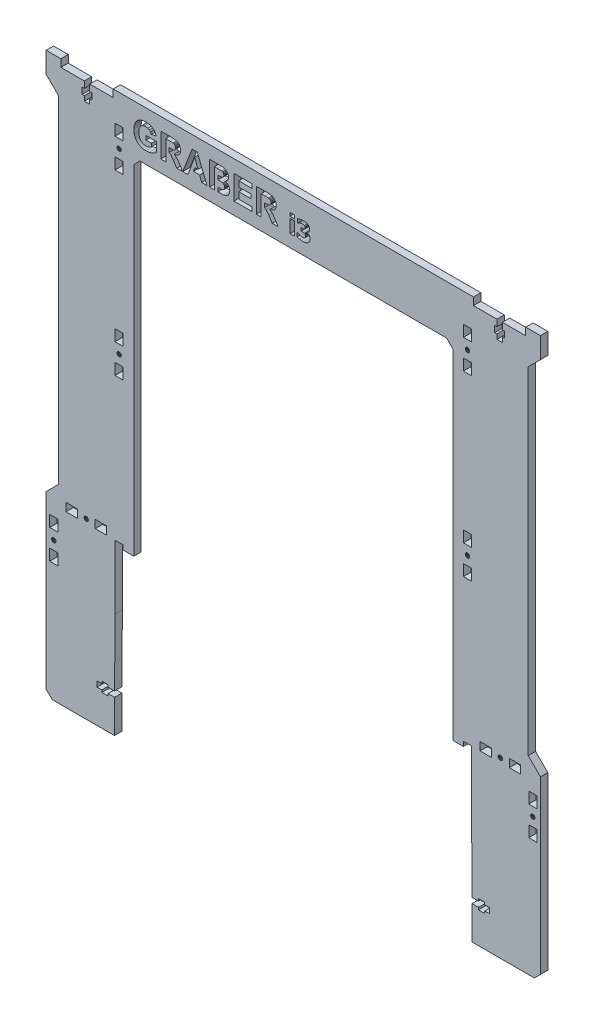
SolidWorks part; units mm, degrees
material "Maple"
ref_plane "Front Plane" through (0, 0, 0) normal (0, 0, 1) x (1, 0, 0)
ref_plane "Top Plane" through (0, 0, 0) normal (0, 1, 0) x (1, 0, 0)
ref_plane "Right Plane" through (0, 0, 0) normal (1, 0, 0) x (0, 0, -1)
sketch "Sketch1" plane through (0, 0, 0) normal (0, 0, 1) x (1, 0, 0)
  line L3495 (502.4777, 83.0503) -> (493.8277, 83.0503)
  line L3496 (509.2276, 34.5503) -> (509.5016, -19.959)
  line L3497 (218.4777, 34.5503) -> (218.4777, 86.741)
  line L3498 (218.4777, 86.741) -> (225.1777, 86.741)
  line L3499 (167.3778, -51.459) -> (162.3778, -46.6507)
  line L3500 (565.3276, -46.459) -> (560.3276, -51.459)
  line L3501 (233.8277, 359.5409) -> (238.8277, 364.5409)
  line L3502 (238.8277, 364.5409) -> (488.8277, 364.5409)
  line L3503 (488.8277, 364.5409) -> (493.8277, 359.5409)
  line L3504 (493.8277, 359.5409) -> (493.8277, 83.0503)
  line L3505 (534.2276, 398.4409) -> (553.3276, 398.4409)
  line L3506 (553.3276, 398.4409) -> (553.3276, 404.5409)
  line L3507 (191.6777, 393.1409) -> (191.6777, 388.0409)
  line L3508 (197.8777, 398.4409) -> (216.9777, 398.4409)
  line L3509 (529.8276, 393.1409) -> (528.0276, 393.1409)
  line L3510 (536.0276, 393.1409) -> (534.2276, 393.1409)
  line L3511 (553.3276, 404.5409) -> (565.3276, 404.5409)
  line L3512 (216.9777, 398.4409) -> (216.9777, 404.5409)
  line L3513 (529.8276, 388.0409) -> (529.8276, 384.0909)
  line L3514 (534.2276, 384.0909) -> (534.2276, 388.0409)
  line L3515 (528.0276, 393.1409) -> (528.0276, 388.0409)
  line L3516 (510.7276, 404.5409) -> (510.7276, 398.4409)
  line L3517 (510.7276, 398.4409) -> (529.8276, 398.4409)
  line L3518 (528.0276, 388.0409) -> (529.8276, 388.0409)
  line L3519 (529.8276, 384.0909) -> (534.2276, 384.0909)
  line L3520 (534.2276, 388.0409) -> (536.0276, 388.0409)
  line L3521 (529.8276, 398.4409) -> (529.8276, 393.1409)
  line L3522 (534.2276, 393.1409) -> (534.2276, 398.4409)
  line L3523 (536.0276, 388.0409) -> (536.0276, 393.1409)
  line L3524 (565.3276, 404.5409) -> (565.3276, 387.5409)
  line L3525 (560.3276, -51.459) -> (509.6276, -51.459)
  line L3526 (199.6777, 393.1409) -> (197.8777, 393.1409)
  line L3527 (193.4777, 398.4409) -> (193.4777, 393.1409)
  line L3528 (197.8777, 388.0409) -> (199.6777, 388.0409)
  line L3529 (197.8777, 393.1409) -> (197.8777, 398.4409)
  line L3530 (193.4777, 384.0909) -> (197.8777, 384.0909)
  line L3531 (199.6777, 388.0409) -> (199.6777, 393.1409)
  line L3532 (193.4777, 388.0409) -> (193.4777, 384.0909)
  line L3533 (197.8777, 384.0909) -> (197.8777, 388.0409)
  line L3534 (193.4777, 393.1409) -> (191.6777, 393.1409)
  line L3535 (191.6777, 388.0409) -> (193.4777, 388.0409)
  line L3536 (162.3778, -46.6507) -> (162.3778, 93.041)
  line L3537 (162.3778, 404.5409) -> (174.3778, 404.5409)
  line L3538 (174.3778, 398.4409) -> (193.4777, 398.4409)
  line L3539 (174.3778, 404.5409) -> (174.3778, 398.4409)
  line L3540 (216.9777, 404.5409) -> (510.7276, 404.5409)
  line L3541 (225.1777, 86.741) -> (225.1777, 83.0503)
  line L3542 (233.8277, 83.0503) -> (233.8277, 359.5409)
  line L3543 (225.1777, 83.0503) -> (233.8277, 83.0503)
  line L3544 (509.2276, 34.5503) -> (509.2276, 86.741)
  line L3545 (509.2276, 86.741) -> (502.4777, 86.741)
  line L3546 (502.4777, 86.741) -> (502.4777, 83.0503)
  line L3547 (218.0277, -51.459) -> (167.3778, -51.459)
  line L3548 (218.4777, 34.5503) -> (218.1695, -19.959)
  line L3549 (162.3778, 93.041) -> (172.3778, 103.041)
  line L3550 (162.3778, 387.5409) -> (162.3778, 404.5409)
  line L3551 (162.3778, 387.5409) -> (172.3778, 377.5409)
  line L3552 (172.3778, 377.5409) -> (172.3778, 103.041)
  line L3553 (565.3276, 93.041) -> (565.3276, -46.459)
  line L3554 (565.3276, 93.041) -> (555.3276, 103.041)
  line L3555 (555.3276, 103.041) -> (555.3276, 377.5409)
  line L3556 (555.3276, 377.5409) -> (565.3276, 387.5409)
  line L3557 (223.1018, 365.9091) -> (222.7286, 366.1955)
  line L3558 (223.3881, 365.536) -> (223.1018, 365.9091)
  line L3559 (223.5681, 365.1015) -> (223.3881, 365.536)
  line L3560 (223.5681, 364.1688) -> (223.6295, 364.6351)
  line L3561 (223.3881, 363.7343) -> (223.5681, 364.1688)
  line L3562 (223.1018, 363.3611) -> (223.3881, 363.7343)
  line L3563 (222.7286, 363.0748) -> (223.1018, 363.3611)
  line L3564 (222.2941, 362.8948) -> (222.7286, 363.0748)
  line L3565 (221.8277, 362.8334) -> (222.2941, 362.8948)
  line L3566 (220.026, 219.5502) -> (220.0874, 219.0839)
  line L3567 (221.3614, 217.8099) -> (221.8277, 217.7485)
  line L3568 (220.9269, 217.9899) -> (221.3614, 217.8099)
  line L3569 (507.568, 364.1688) -> (507.6294, 364.6351)
  line L3570 (507.388, 363.7343) -> (507.568, 364.1688)
  line L3571 (507.1017, 363.3611) -> (507.388, 363.7343)
  line L3572 (506.7285, 363.0748) -> (507.1017, 363.3611)
  line L3573 (506.294, 362.8948) -> (506.7285, 363.0748)
  line L3574 (505.8277, 362.8334) -> (506.294, 362.8948)
  line L3575 (220.0874, 365.1015) -> (220.026, 364.6351)
  line L3576 (220.2674, 365.536) -> (220.0874, 365.1015)
  line L3577 (187.7778, 86.791) -> (187.7778, 93.3909)
  line L3578 (202.3777, 93.3909) -> (202.3777, 86.791)
  line L3579 (202.3777, 86.791) -> (211.5777, 86.791)
  line L3580 (562.3776, 45.291) -> (562.3776, 54.491)
  line L3581 (218.5277, 357.3351) -> (218.5277, 348.1351)
  line L3582 (225.1277, 371.9351) -> (225.1277, 381.1351)
  line L3583 (559.544, 63.5313) -> (559.0776, 63.5927)
  line L3584 (558.1768, 60.2306) -> (558.6113, 60.0506)
  line L3585 (170.3181, 61.3246) -> (170.3795, 61.791)
  line L3586 (167.0174, 62.6918) -> (166.8374, 62.2573)
  line L3587 (168.5778, 63.5927) -> (168.1114, 63.5313)
  line L3588 (169.8518, 63.065) -> (169.4786, 63.3513)
  line L3589 (193.3374, 89.6246) -> (193.5174, 89.1901)
  line L3590 (195.9786, 91.6513) -> (195.5441, 91.8313)
  line L3591 (560.8794, 61.791) -> (560.818, 62.2573)
  line L3592 (170.3795, 61.791) -> (170.3181, 62.2573)
  line L3593 (166.8374, 62.2573) -> (166.776, 61.791)
  line L3594 (559.0776, 63.5927) -> (558.6113, 63.5313)
  line L3595 (169.4786, 63.3513) -> (169.0441, 63.5313)
  line L3596 (167.3037, 60.5169) -> (167.6769, 60.2306)
  line L3597 (559.0776, 59.9892) -> (559.544, 60.0506)
  line L3598 (168.1114, 60.0506) -> (168.5778, 59.9892)
  line L3599 (558.6113, 63.5313) -> (558.1768, 63.3513)
  line L3600 (559.9785, 63.3513) -> (559.544, 63.5313)
  line L3601 (170.1381, 62.6918) -> (169.8518, 63.065)
  line L3602 (560.818, 61.3246) -> (560.8794, 61.791)
  line L3603 (271.9766, 388.6925) -> (271.8953, 387.6341)
  line L3604 (271.8953, 387.6341) -> (271.6513, 386.672)
  line L3605 (271.6513, 386.672) -> (271.2447, 385.8064)
  line L3606 (271.2447, 385.8064) -> (270.6755, 385.0372)
  line L3607 (225.1277, 381.1351) -> (218.5277, 381.1351)
  line L3608 (218.5277, 381.1351) -> (218.5277, 371.9351)
  line L3609 (218.5277, 371.9351) -> (225.1277, 371.9351)
  line L3610 (218.5277, 348.1351) -> (225.1277, 348.1351)
  line L3611 (225.1277, 348.1351) -> (225.1277, 357.3351)
  line L3612 (225.1277, 357.3351) -> (218.5277, 357.3351)
  line L3613 (225.1277, 236.0502) -> (218.5277, 236.0502)
  line L3614 (218.5277, 236.0502) -> (218.5277, 226.8502)
  line L3615 (218.5277, 226.8502) -> (225.1277, 226.8502)
  line L3616 (218.5277, 203.0502) -> (225.1277, 203.0502)
  line L3617 (225.1277, 203.0502) -> (225.1277, 212.2502)
  line L3618 (225.1277, 212.2502) -> (218.5277, 212.2502)
  line L3619 (218.5277, 212.2502) -> (218.5277, 203.0502)
  line L3620 (533.9016, 91.365) -> (533.5285, 91.6513)
  line L3621 (557.8036, 63.065) -> (557.5173, 62.6918)
  line L3622 (196.8181, 90.5573) -> (196.6381, 90.9918)
  line L3623 (195.0777, 88.2892) -> (195.5441, 88.3506)
  line L3624 (193.8037, 88.8169) -> (194.1769, 88.5306)
  line L3625 (532.6276, 91.8927) -> (532.1613, 91.8313)
  line L3626 (531.3536, 91.365) -> (531.0673, 90.9918)
  line L3627 (532.1613, 91.8313) -> (531.7268, 91.6513)
  line L3628 (557.8036, 60.5169) -> (558.1768, 60.2306)
  line L3629 (559.9785, 60.2306) -> (560.3516, 60.5169)
  line L3630 (560.818, 62.2573) -> (560.638, 62.6918)
  line L3631 (165.2778, 45.291) -> (171.8778, 45.291)
  line L3632 (171.8778, 69.091) -> (171.8778, 78.291)
  line L3633 (171.8778, 78.291) -> (165.2778, 78.291)
  line L3634 (165.2778, 78.291) -> (165.2778, 69.091)
  line L3635 (165.2778, 69.091) -> (171.8778, 69.091)
  line L3636 (187.7778, 93.3909) -> (178.5778, 93.3909)
  line L3637 (178.5778, 93.3909) -> (178.5778, 86.791)
  line L3638 (178.5778, 86.791) -> (187.7778, 86.791)
  line L3639 (220.9269, 366.1955) -> (220.5537, 365.9091)
  line L3640 (221.3614, 366.3755) -> (220.9269, 366.1955)
  line L3641 (221.8277, 366.4369) -> (221.3614, 366.3755)
  line L3642 (220.026, 364.6351) -> (220.0874, 364.1688)
  line L3643 (221.3614, 362.8948) -> (221.8277, 362.8334)
  line L3644 (220.9269, 363.0748) -> (221.3614, 362.8948)
  line L3645 (220.5537, 363.3611) -> (220.9269, 363.0748)
  line L3646 (220.2674, 363.7343) -> (220.5537, 363.3611)
  line L3647 (220.0874, 364.1688) -> (220.2674, 363.7343)
  line L3648 (223.6295, 364.6351) -> (223.5681, 365.1015)
  line L3649 (222.2941, 366.3755) -> (221.8277, 366.4369)
  line L3650 (222.7286, 366.1955) -> (222.2941, 366.3755)
  line L3651 (220.5537, 218.2762) -> (220.9269, 217.9899)
  line L3652 (220.2674, 218.6493) -> (220.5537, 218.2762)
  line L3653 (220.0874, 219.0839) -> (220.2674, 218.6493)
  line L3654 (223.6295, 219.5502) -> (223.5681, 220.0165)
  line L3655 (222.2941, 221.2905) -> (221.8277, 221.3519)
  line L3656 (222.7286, 221.1106) -> (222.2941, 221.2905)
  line L3657 (223.1018, 220.8242) -> (222.7286, 221.1106)
  line L3658 (223.3881, 220.4511) -> (223.1018, 220.8242)
  line L3659 (223.5681, 220.0165) -> (223.3881, 220.4511)
  line L3660 (220.0874, 220.0165) -> (220.026, 219.5502)
  line L3661 (220.2674, 220.4511) -> (220.0874, 220.0165)
  line L3662 (220.5537, 220.8242) -> (220.2674, 220.4511)
  line L3663 (220.9269, 221.1106) -> (220.5537, 220.8242)
  line L3664 (221.3614, 221.2905) -> (220.9269, 221.1106)
  line L3665 (221.8277, 221.3519) -> (221.3614, 221.2905)
  line L3666 (223.5681, 219.0839) -> (223.6295, 219.5502)
  line L3667 (223.3881, 218.6493) -> (223.5681, 219.0839)
  line L3668 (516.1276, 93.3909) -> (516.1276, 86.791)
  line L3669 (516.1276, 86.791) -> (525.3276, 86.791)
  line L3670 (525.3276, 86.791) -> (525.3276, 93.3909)
  line L3671 (525.3276, 93.3909) -> (516.1276, 93.3909)
  line L3672 (539.9276, 86.791) -> (549.1276, 86.791)
  line L3673 (167.3037, 63.065) -> (167.0174, 62.6918)
  line L3674 (166.776, 61.791) -> (166.8374, 61.3246)
  line L3675 (168.5778, 59.9892) -> (169.0441, 60.0506)
  line L3676 (169.0441, 63.5313) -> (168.5778, 63.5927)
  line L3677 (168.1114, 63.5313) -> (167.6769, 63.3513)
  line L3678 (196.3518, 88.8169) -> (196.6381, 89.1901)
  line L3679 (194.1769, 91.6513) -> (193.8037, 91.365)
  line L3680 (211.5777, 86.791) -> (211.5777, 93.3909)
  line L3681 (549.1276, 86.791) -> (549.1276, 93.3909)
  line L3682 (549.1276, 93.3909) -> (539.9276, 93.3909)
  line L3683 (539.9276, 93.3909) -> (539.9276, 86.791)
  line L3684 (562.3776, 78.291) -> (555.7776, 78.291)
  line L3685 (171.8778, 54.491) -> (165.2778, 54.491)
  line L3686 (165.2778, 54.491) -> (165.2778, 45.291)
  line L3687 (558.1768, 63.3513) -> (557.8036, 63.065)
  line L3688 (169.4786, 60.2306) -> (169.8518, 60.5169)
  line L3689 (557.2759, 61.791) -> (557.3373, 61.3246)
  line L3690 (560.3516, 60.5169) -> (560.638, 60.8901)
  line L3691 (557.5173, 62.6918) -> (557.3373, 62.2573)
  line L3692 (560.3516, 63.065) -> (559.9785, 63.3513)
  line L3693 (558.6113, 60.0506) -> (559.0776, 59.9892)
  line L3694 (507.568, 220.0165) -> (507.388, 220.4511)
  line L3695 (504.0873, 220.0165) -> (504.0259, 219.5502)
  line L3696 (505.8277, 221.3519) -> (505.3613, 221.2905)
  line L3697 (507.568, 365.1015) -> (507.388, 365.536)
  line L3698 (507.6294, 364.6351) -> (507.568, 365.1015)
  line L3699 (506.294, 366.3755) -> (505.8277, 366.4369)
  line L3700 (506.7285, 366.1955) -> (506.294, 366.3755)
  line L3701 (507.1017, 365.9091) -> (506.7285, 366.1955)
  line L3702 (507.388, 365.536) -> (507.1017, 365.9091)
  line L3703 (504.2673, 363.7343) -> (504.5536, 363.3611)
  line L3704 (504.0259, 364.6351) -> (504.0873, 364.1688)
  line L3705 (505.8277, 366.4369) -> (505.3613, 366.3755)
  line L3706 (504.2673, 365.536) -> (504.0873, 365.1015)
  line L3707 (504.0873, 365.1015) -> (504.0259, 364.6351)
  line L3708 (505.3613, 366.3755) -> (504.9268, 366.1955)
  line L3709 (504.5536, 365.9091) -> (504.2673, 365.536)
  line L3710 (504.9268, 366.1955) -> (504.5536, 365.9091)
  line L3711 (505.3613, 362.8948) -> (505.8277, 362.8334)
  line L3712 (504.5536, 363.3611) -> (504.9268, 363.0748)
  line L3713 (504.0873, 364.1688) -> (504.2673, 363.7343)
  line L3714 (504.9268, 363.0748) -> (505.3613, 362.8948)
  line L3715 (225.1277, 226.8502) -> (225.1277, 236.0502)
  line L3716 (502.5276, 212.2502) -> (502.5276, 203.0502)
  line L3717 (509.1277, 236.0502) -> (502.5276, 236.0502)
  line L3718 (502.5276, 381.1351) -> (502.5276, 371.9351)
  line L3719 (502.5276, 371.9351) -> (509.1277, 371.9351)
  line L3720 (509.1277, 381.1351) -> (502.5276, 381.1351)
  line L3721 (509.1277, 226.8502) -> (509.1277, 236.0502)
  line L3722 (509.1277, 212.2502) -> (502.5276, 212.2502)
  line L3723 (502.5276, 226.8502) -> (509.1277, 226.8502)
  line L3724 (502.5276, 203.0502) -> (509.1277, 203.0502)
  line L3725 (502.5276, 236.0502) -> (502.5276, 226.8502)
  line L3726 (509.1277, 203.0502) -> (509.1277, 212.2502)
  line L3727 (195.5441, 88.3506) -> (195.9786, 88.5306)
  line L3728 (195.9786, 88.5306) -> (196.3518, 88.8169)
  line L3729 (531.0673, 90.9918) -> (530.8873, 90.5573)
  line L3730 (557.3373, 62.2573) -> (557.2759, 61.791)
  line L3731 (171.8778, 45.291) -> (171.8778, 54.491)
  line L3732 (211.5777, 93.3909) -> (202.3777, 93.3909)
  line L3733 (236.7016, 392.0091) -> (237.7186, 392.855)
  line L3734 (237.7186, 392.855) -> (238.8847, 393.5617)
  line L3735 (238.8847, 393.5617) -> (239.8883, 393.9901)
  line L3736 (239.8883, 393.9901) -> (241.0075, 394.2961)
  line L3737 (241.0075, 394.2961) -> (243.593, 394.5409)
  line L3738 (243.593, 394.5409) -> (245.3238, 394.4449)
  line L3739 (245.3238, 394.4449) -> (246.8542, 394.1569)
  line L3740 (246.8542, 394.1569) -> (248.1843, 393.677)
  line L3741 (248.1843, 393.677) -> (249.314, 393.005)
  line L3742 (249.314, 393.005) -> (250.2517, 392.1637)
  line L3743 (250.2517, 392.1637) -> (251.0058, 391.1757)
  line L3744 (251.0058, 391.1757) -> (251.5763, 390.041)
  line L3745 (251.5763, 390.041) -> (251.9632, 388.7596)
  line L3746 (251.9632, 388.7596) -> (248.0196, 388.0218)
  line L3747 (248.0196, 388.0218) -> (247.421, 389.3179)
  line L3748 (247.421, 389.3179) -> (246.4568, 390.3089)
  line L3749 (246.4568, 390.3089) -> (245.1674, 390.9376)
  line L3750 (245.1674, 390.9376) -> (243.593, 391.1472)
  line L3751 (243.593, 391.1472) -> (242.3585, 391.0441)
  line L3752 (242.3585, 391.0441) -> (241.2573, 390.7347)
  line L3753 (241.2573, 390.7347) -> (240.2894, 390.2192)
  line L3754 (240.2894, 390.2192) -> (239.4548, 389.4973)
  line L3755 (239.4548, 389.4973) -> (238.7829, 388.5726)
  line L3756 (238.7829, 388.5726) -> (238.3029, 387.4484)
  line L3757 (238.3029, 387.4484) -> (238.0149, 386.1246)
  line L3758 (238.0149, 386.1246) -> (237.919, 384.6013)
  line L3759 (237.919, 384.6013) -> (238.0162, 382.9602)
  line L3760 (238.0162, 382.9602) -> (238.308, 381.5379)
  line L3761 (238.308, 381.5379) -> (238.7942, 380.3344)
  line L3762 (238.7942, 380.3344) -> (239.475, 379.3498)
  line L3763 (239.475, 379.3498) -> (240.3133, 378.5839)
  line L3764 (240.3133, 378.5839) -> (241.2724, 378.0369)
  line L3765 (241.2724, 378.0369) -> (242.3522, 377.7087)
  line L3766 (242.3522, 377.7087) -> (243.5528, 377.5993)
  line L3767 (243.5528, 377.5993) -> (244.8019, 377.7217)
  line L3768 (244.8019, 377.7217) -> (246.0544, 378.0889)
  line L3769 (246.0544, 378.0889) -> (247.2198, 378.6305)
  line L3770 (247.2198, 378.6305) -> (248.2073, 379.276)
  line L3771 (248.2073, 379.276) -> (248.2073, 381.771)
  line L3772 (248.2073, 381.771) -> (243.6601, 381.771)
  line L3773 (243.6601, 381.771) -> (243.6601, 385.0842)
  line L3774 (243.6601, 385.0842) -> (252.2181, 385.0842)
  line L3775 (252.2181, 385.0842) -> (252.2181, 377.2505)
  line L3776 (252.2181, 377.2505) -> (250.6906, 376.1154)
  line L3777 (250.6906, 376.1154) -> (248.6031, 375.1244)
  line L3778 (248.6031, 375.1244) -> (246.2204, 374.4353)
  line L3779 (246.2204, 374.4353) -> (243.8076, 374.2056)
  line L3780 (243.8076, 374.2056) -> (242.3145, 374.2865)
  line L3781 (242.3145, 374.2865) -> (240.9203, 374.5292)
  line L3782 (240.9203, 374.5292) -> (239.625, 374.9337)
  line L3783 (239.625, 374.9337) -> (238.4287, 375.5)
  line L3784 (238.4287, 375.5) -> (237.3531, 376.2168)
  line L3785 (237.3531, 376.2168) -> (236.42, 377.0728)
  line L3786 (236.42, 377.0728) -> (235.6294, 378.0679)
  line L3787 (235.6294, 378.0679) -> (234.9813, 379.2022)
  line L3788 (234.9813, 379.2022) -> (234.4766, 380.4325)
  line L3789 (234.4766, 380.4325) -> (234.1161, 381.7156)
  line L3790 (234.1161, 381.7156) -> (233.8277, 384.4403)
  line L3791 (233.8277, 384.4403) -> (233.9082, 385.9334)
  line L3792 (233.9082, 385.9334) -> (234.1497, 387.3411)
  line L3793 (234.1497, 387.3411) -> (234.5521, 388.6632)
  line L3794 (234.5521, 388.6632) -> (235.1155, 389.8997)
  line L3795 (235.1155, 389.8997) -> (235.8339, 391.024)
  line L3796 (235.8339, 391.024) -> (236.7016, 392.0091)
  line L3797 (220.5537, 365.9091) -> (220.2674, 365.536)
  line L3798 (223.1018, 218.2762) -> (223.3881, 218.6493)
  line L3799 (222.7286, 217.9899) -> (223.1018, 218.2762)
  line L3800 (222.2941, 217.8099) -> (222.7286, 217.9899)
  line L3801 (221.8277, 217.7485) -> (222.2941, 217.8099)
  line L3802 (307.0538, 374.6751) -> (302.342, 374.5431)
  line L3803 (302.342, 377.8541) -> (302.342, 374.5431)
  line L3804 (302.342, 377.8541) -> (303.2174, 377.8541)
  line L3805 (303.2174, 377.8541) -> (305.9404, 377.9749)
  line L3806 (305.9404, 377.9749) -> (306.7436, 378.2515)
  line L3807 (306.7436, 378.2515) -> (307.3824, 378.7596)
  line L3808 (307.3824, 378.7596) -> (307.7999, 379.4889)
  line L3809 (307.7999, 379.4889) -> (307.9391, 380.4296)
  line L3810 (307.9391, 380.4296) -> (307.8318, 381.2478)
  line L3811 (307.8318, 381.2478) -> (307.5098, 381.9319)
  line L3812 (307.5098, 381.9319) -> (306.985, 382.4651)
  line L3813 (306.985, 382.4651) -> (306.2691, 382.8307)
  line L3814 (306.2691, 382.8307) -> (304.983, 383.0419)
  line L3815 (304.983, 383.0419) -> (302.7479, 383.1123)
  line L3816 (302.7479, 383.1123) -> (302.342, 383.1123)
  line L3817 (302.342, 383.1123) -> (302.342, 386.3899)
  line L3818 (302.342, 386.3899) -> (305.0283, 386.4524)
  line L3819 (305.0283, 386.4524) -> (305.9387, 386.6888)
  line L3820 (305.9387, 386.6888) -> (306.6312, 387.1566)
  line L3821 (306.6312, 387.1566) -> (307.0689, 387.8323)
  line L3822 (307.0689, 387.8323) -> (307.2147, 388.6925)
  line L3823 (307.2147, 388.6925) -> (307.089, 389.5191)
  line L3824 (307.089, 389.5191) -> (306.7117, 390.1747)
  line L3825 (306.7117, 390.1747) -> (306.0863, 390.6325)
  line L3826 (306.0863, 390.6325) -> (305.2161, 390.8655)
  line L3827 (305.2161, 390.8655) -> (301.8224, 390.9326)
  line L3828 (301.8224, 390.9326) -> (299.542, 390.9326)
  line L3829 (299.542, 390.9326) -> (299.542, 374.5409)
  line L3830 (299.542, 374.5409) -> (295.5715, 374.5409)
  line L3831 (295.5715, 374.5409) -> (295.5715, 394.2056)
  line L3832 (295.5715, 394.2056) -> (303.432, 394.2056)
  line L3833 (303.432, 394.2056) -> (306.9129, 394.0111)
  line L3834 (306.9129, 394.0111) -> (307.9994, 393.7109)
  line L3835 (307.9994, 393.7109) -> (308.9652, 393.1995)
  line L3836 (308.9652, 393.1995) -> (309.7952, 392.4802)
  line L3837 (309.7952, 392.4802) -> (310.4743, 391.5563)
  line L3838 (310.4743, 391.5563) -> (310.927, 390.4681)
  line L3839 (310.927, 390.4681) -> (311.0779, 389.2559)
  line L3840 (311.0779, 389.2559) -> (310.8918, 387.9313)
  line L3841 (310.8918, 387.9313) -> (310.3334, 386.7207)
  line L3842 (310.3334, 386.7207) -> (309.4565, 385.7113)
  line L3843 (309.4565, 385.7113) -> (308.3147, 384.9903)
  line L3844 (308.3147, 384.9903) -> (309.9042, 384.2827)
  line L3845 (309.9042, 384.2827) -> (311.0779, 383.2062)
  line L3846 (311.0779, 383.2062) -> (311.8023, 381.8347)
  line L3847 (311.8023, 381.8347) -> (312.0437, 380.2418)
  line L3848 (312.0437, 380.2418) -> (311.8878, 378.9189)
  line L3849 (311.8878, 378.9189) -> (311.42, 377.6328)
  line L3850 (311.42, 377.6328) -> (310.6822, 376.4926)
  line L3851 (310.6822, 376.4926) -> (309.7164, 375.6073)
  line L3852 (309.7164, 375.6073) -> (308.5108, 374.9953)
  line L3853 (308.5108, 374.9953) -> (307.0538, 374.6751)
  line L3854 (341.1215, 382.2136) -> (340.5078, 382.5288)
  line L3855 (340.5043, 385.889) -> (340.5078, 382.5288)
  line L3856 (340.5043, 385.889) -> (340.642, 385.889)
  line L3857 (340.642, 385.889) -> (342.9625, 385.9494)
  line L3858 (342.9625, 385.9494) -> (344.21, 386.1305)
  line L3859 (344.21, 386.1305) -> (344.8438, 386.4591)
  line L3860 (344.8438, 386.4591) -> (345.3234, 386.9621)
  line L3861 (345.3234, 386.9621) -> (345.6252, 387.6261)
  line L3862 (345.6252, 387.6261) -> (345.7258, 388.4376)
  line L3863 (345.7258, 388.4376) -> (345.5933, 389.3347)
  line L3864 (345.5933, 389.3347) -> (345.1959, 390.0406)
  line L3865 (345.1959, 390.0406) -> (344.5571, 390.5386)
  line L3866 (344.5571, 390.5386) -> (343.7003, 390.8119)
  line L3867 (343.7003, 390.8119) -> (340.8029, 390.8789)
  line L3868 (340.8029, 390.8789) -> (337.7043, 390.8789)
  line L3869 (337.7043, 390.8789) -> (337.7043, 374.5409)
  line L3870 (337.7043, 374.5409) -> (333.7338, 374.5409)
  line L3871 (333.7338, 374.5409) -> (333.7338, 394.2056)
  line L3872 (333.7338, 394.2056) -> (342.0906, 394.2056)
  line L3873 (342.0906, 394.2056) -> (344.812, 394.0731)
  line L3874 (344.812, 394.0731) -> (346.6715, 393.6757)
  line L3875 (346.6715, 393.6757) -> (347.9575, 392.9396)
  line L3876 (347.9575, 392.9396) -> (348.9585, 391.7911)
  line L3877 (348.9585, 391.7911) -> (349.6024, 390.339)
  line L3878 (349.6024, 390.339) -> (349.817, 388.6925)
  line L3879 (349.817, 388.6925) -> (349.7357, 387.6341)
  line L3880 (349.7357, 387.6341) -> (349.4917, 386.672)
  line L3881 (349.4917, 386.672) -> (349.0851, 385.8064)
  line L3882 (349.0851, 385.8064) -> (348.5159, 385.0372)
  line L3883 (348.5159, 385.0372) -> (347.7848, 384.3829)
  line L3884 (347.7848, 384.3829) -> (346.8928, 383.8618)
  line L3885 (346.8928, 383.8618) -> (345.8398, 383.4741)
  line L3886 (345.8398, 383.4741) -> (344.6259, 383.2197)
  line L3887 (344.6259, 383.2197) -> (345.8012, 382.4316)
  line L3888 (345.8012, 382.4316) -> (346.7519, 381.5698)
  line L3889 (346.7519, 381.5698) -> (347.7362, 380.3223)
  line L3890 (347.7362, 380.3223) -> (349.0122, 378.3773)
  line L3891 (349.0122, 378.3773) -> (351.4133, 374.5409)
  line L3892 (351.4133, 374.5409) -> (346.6648, 374.5409)
  line L3893 (346.6648, 374.5409) -> (343.7942, 378.8199)
  line L3894 (343.7942, 378.8199) -> (341.7016, 381.7106)
  line L3895 (341.7016, 381.7106) -> (341.1215, 382.2136)
  line L3896 (282.354, 379.0077) -> (283.5747, 382.3209)
  line L3897 (283.5747, 382.3209) -> (286.1416, 382.3209)
  line L3898 (286.1416, 382.3209) -> (283.432, 389.618)
  line L3899 (283.432, 389.618) -> (277.9324, 374.5409)
  line L3900 (277.9324, 374.5409) -> (273.7204, 374.5409)
  line L3901 (273.7204, 374.5409) -> (281.3797, 394.2056)
  line L3902 (281.3797, 394.2056) -> (285.5782, 394.2056)
  line L3903 (285.5782, 394.2056) -> (293.4522, 374.5409)
  line L3904 (293.4522, 374.5409) -> (289.1329, 374.5409)
  line L3905 (289.1329, 374.5409) -> (287.4159, 379.0077)
  line L3906 (287.4159, 379.0077) -> (282.354, 379.0077)
  line L3907 (555.7776, 45.291) -> (562.3776, 45.291)
  line L3908 (555.7776, 54.491) -> (555.7776, 45.291)
  line L3909 (562.3776, 54.491) -> (555.7776, 54.491)
  line L3910 (560.638, 62.6918) -> (560.3516, 63.065)
  line L3911 (560.638, 60.8901) -> (560.818, 61.3246)
  line L3912 (559.544, 60.0506) -> (559.9785, 60.2306)
  line L3913 (557.5173, 60.8901) -> (557.8036, 60.5169)
  line L3914 (557.3373, 61.3246) -> (557.5173, 60.8901)
  line L3915 (170.1381, 60.8901) -> (170.3181, 61.3246)
  line L3916 (169.8518, 60.5169) -> (170.1381, 60.8901)
  line L3917 (169.0441, 60.0506) -> (169.4786, 60.2306)
  line L3918 (167.6769, 60.2306) -> (168.1114, 60.0506)
  line L3919 (167.0174, 60.8901) -> (167.3037, 60.5169)
  line L3920 (166.8374, 61.3246) -> (167.0174, 60.8901)
  line L3921 (167.6769, 63.3513) -> (167.3037, 63.065)
  line L3922 (170.3181, 62.2573) -> (170.1381, 62.6918)
  line L3923 (193.276, 90.0909) -> (193.3374, 89.6246)
  line L3924 (193.3374, 90.5573) -> (193.276, 90.0909)
  line L3925 (193.5174, 90.9918) -> (193.3374, 90.5573)
  line L3926 (193.8037, 91.365) -> (193.5174, 90.9918)
  line L3927 (194.6114, 91.8313) -> (194.1769, 91.6513)
  line L3928 (195.0777, 91.8927) -> (194.6114, 91.8313)
  line L3929 (195.5441, 91.8313) -> (195.0777, 91.8927)
  line L3930 (196.3518, 91.365) -> (195.9786, 91.6513)
  line L3931 (196.6381, 90.9918) -> (196.3518, 91.365)
  line L3932 (196.8795, 90.0909) -> (196.8181, 90.5573)
  line L3933 (196.8181, 89.6246) -> (196.8795, 90.0909)
  line L3934 (196.6381, 89.1901) -> (196.8181, 89.6246)
  line L3935 (194.6114, 88.3506) -> (195.0777, 88.2892)
  line L3936 (194.1769, 88.5306) -> (194.6114, 88.3506)
  line L3937 (193.5174, 89.1901) -> (193.8037, 88.8169)
  line L3938 (330.3536, 374.5409) -> (315.3972, 374.5409)
  line L3939 (315.3972, 374.5409) -> (315.3972, 394.2056)
  line L3940 (315.3972, 394.2056) -> (329.978, 394.2056)
  line L3941 (329.978, 394.2056) -> (329.978, 390.8789)
  line L3942 (329.978, 390.8789) -> (319.3676, 390.8789)
  line L3943 (319.3676, 390.8789) -> (319.3676, 386.5195)
  line L3944 (319.3676, 386.5195) -> (329.2402, 386.5195)
  line L3945 (329.2402, 386.5195) -> (329.2402, 383.2062)
  line L3946 (329.2402, 383.2062) -> (319.3676, 383.2062)
  line L3947 (319.3676, 383.2062) -> (319.3676, 377.8541)
  line L3948 (319.3676, 377.8541) -> (330.3536, 377.8541)
  line L3949 (330.3536, 377.8541) -> (330.3536, 374.5409)
  line L3950 (534.188, 90.9918) -> (533.9016, 91.365)
  line L3951 (534.368, 90.5573) -> (534.188, 90.9918)
  line L3952 (534.4294, 90.0909) -> (534.368, 90.5573)
  line L3953 (534.368, 89.6246) -> (534.4294, 90.0909)
  line L3954 (534.188, 89.1901) -> (534.368, 89.6246)
  line L3955 (533.9016, 88.8169) -> (534.188, 89.1901)
  line L3956 (533.5285, 88.5306) -> (533.9016, 88.8169)
  line L3957 (533.094, 88.3506) -> (533.5285, 88.5306)
  line L3958 (532.6276, 88.2892) -> (533.094, 88.3506)
  line L3959 (532.1613, 88.3506) -> (532.6276, 88.2892)
  line L3960 (531.7268, 88.5306) -> (532.1613, 88.3506)
  line L3961 (531.3536, 88.8169) -> (531.7268, 88.5306)
  line L3962 (531.0673, 89.1901) -> (531.3536, 88.8169)
  line L3963 (530.8873, 89.6246) -> (531.0673, 89.1901)
  line L3964 (530.8259, 90.0909) -> (530.8873, 89.6246)
  line L3965 (530.8873, 90.5573) -> (530.8259, 90.0909)
  line L3966 (531.7268, 91.6513) -> (531.3536, 91.365)
  line L3967 (533.094, 91.8313) -> (532.6276, 91.8927)
  line L3968 (533.5285, 91.6513) -> (533.094, 91.8313)
  line L3969 (562.3776, 69.091) -> (562.3776, 78.291)
  line L3970 (555.7776, 69.091) -> (562.3776, 69.091)
  line L3971 (555.7776, 78.291) -> (555.7776, 69.091)
  line L3972 (507.6294, 219.5502) -> (507.568, 220.0165)
  line L3973 (507.568, 219.0839) -> (507.6294, 219.5502)
  line L3974 (507.388, 218.6493) -> (507.568, 219.0839)
  line L3975 (507.1017, 218.2762) -> (507.388, 218.6493)
  line L3976 (506.7285, 217.9899) -> (507.1017, 218.2762)
  line L3977 (506.294, 217.8099) -> (506.7285, 217.9899)
  line L3978 (505.8277, 217.7485) -> (506.294, 217.8099)
  line L3979 (505.3613, 217.8099) -> (505.8277, 217.7485)
  line L3980 (504.9268, 217.9899) -> (505.3613, 217.8099)
  line L3981 (504.5536, 218.2762) -> (504.9268, 217.9899)
  line L3982 (504.2673, 218.6493) -> (504.5536, 218.2762)
  line L3983 (504.0873, 219.0839) -> (504.2673, 218.6493)
  line L3984 (504.0259, 219.5502) -> (504.0873, 219.0839)
  line L3985 (504.2673, 220.4511) -> (504.0873, 220.0165)
  line L3986 (504.5536, 220.8242) -> (504.2673, 220.4511)
  line L3987 (504.9268, 221.1106) -> (504.5536, 220.8242)
  line L3988 (505.3613, 221.2905) -> (504.9268, 221.1106)
  line L3989 (506.294, 221.2905) -> (505.8277, 221.3519)
  line L3990 (506.7285, 221.1106) -> (506.294, 221.2905)
  line L3991 (507.1017, 220.8242) -> (506.7285, 221.1106)
  line L3992 (507.388, 220.4511) -> (507.1017, 220.8242)
  line L3993 (509.1277, 371.9351) -> (509.1277, 381.1351)
  line L3994 (509.1277, 357.3351) -> (502.5276, 357.3351)
  line L3995 (509.1277, 348.1351) -> (509.1277, 357.3351)
  line L3996 (502.5276, 348.1351) -> (509.1277, 348.1351)
  line L3997 (502.5276, 357.3351) -> (502.5276, 348.1351)
  line L3998 (263.2811, 382.2136) -> (262.6674, 382.5288)
  line L3999 (262.6674, 382.5288) -> (262.6674, 385.889)
  line L4000 (262.6674, 385.889) -> (262.8016, 385.889)
  line L4001 (262.8016, 385.889) -> (265.1222, 385.9494)
  line L4002 (265.1222, 385.9494) -> (266.3697, 386.1305)
  line L4003 (266.3697, 386.1305) -> (267.0035, 386.4591)
  line L4004 (267.0035, 386.4591) -> (267.483, 386.9621)
  line L4005 (267.483, 386.9621) -> (267.7848, 387.6261)
  line L4006 (267.7848, 387.6261) -> (267.8854, 388.4376)
  line L4007 (267.8854, 388.4376) -> (267.753, 389.3347)
  line L4008 (267.753, 389.3347) -> (267.3556, 390.0406)
  line L4009 (267.3556, 390.0406) -> (266.7167, 390.5386)
  line L4010 (266.7167, 390.5386) -> (265.8599, 390.8119)
  line L4011 (265.8599, 390.8119) -> (262.9625, 390.8789)
  line L4012 (262.9625, 390.8789) -> (259.864, 390.8789)
  line L4013 (259.864, 390.8789) -> (259.864, 374.5409)
  line L4014 (259.864, 374.5409) -> (255.8935, 374.5409)
  line L4015 (255.8935, 374.5409) -> (255.8935, 394.2056)
  line L4016 (255.8935, 394.2056) -> (264.2503, 394.2056)
  line L4017 (264.2503, 394.2056) -> (266.9716, 394.0731)
  line L4018 (266.9716, 394.0731) -> (268.8311, 393.6757)
  line L4019 (268.8311, 393.6757) -> (270.1171, 392.9396)
  line L4020 (270.1171, 392.9396) -> (271.1181, 391.7911)
  line L4021 (271.1181, 391.7911) -> (271.762, 390.339)
  line L4022 (271.762, 390.339) -> (271.9766, 388.6925)
  line L4023 (270.6755, 385.0372) -> (269.9444, 384.3829)
  line L4024 (269.9444, 384.3829) -> (269.0524, 383.8618)
  line L4025 (269.0524, 383.8618) -> (267.9994, 383.4741)
  line L4026 (267.9994, 383.4741) -> (266.7855, 383.2197)
  line L4027 (266.7855, 383.2197) -> (267.9609, 382.4316)
  line L4028 (267.9609, 382.4316) -> (268.9116, 381.5698)
  line L4029 (268.9116, 381.5698) -> (269.8958, 380.3223)
  line L4030 (269.8958, 380.3223) -> (271.1718, 378.3773)
  line L4031 (271.1718, 378.3773) -> (273.5729, 374.5409)
  line L4032 (273.5729, 374.5409) -> (268.8244, 374.5409)
  line L4033 (268.8244, 374.5409) -> (265.9538, 378.8199)
  line L4034 (265.9538, 378.8199) -> (263.8613, 381.7106)
  line L4035 (263.8613, 381.7106) -> (263.2811, 382.2136)
  line L4036 (364.7841, 386.8302) -> (361.24, 386.8302)
  line L4037 (361.24, 386.8302) -> (361.24, 389.4451)
  line L4038 (361.24, 389.4451) -> (364.7841, 389.4451)
  line L4039 (364.7841, 389.4451) -> (364.7841, 386.8302)
  line L4040 (361.3358, 374.5409) -> (361.3358, 385.2976)
  line L4041 (361.3358, 385.2976) -> (364.6883, 385.2976)
  line L4042 (364.6883, 385.2976) -> (364.6883, 374.5409)
  line L4043 (364.6883, 374.5409) -> (361.3358, 374.5409)
  line L4044 (371.9105, 389.1003) -> (373.0995, 389.0452)
  line L4045 (373.0995, 389.0452) -> (374.1184, 388.88)
  line L4046 (374.1184, 388.88) -> (374.984, 388.6094)
  line L4047 (374.984, 388.6094) -> (375.7132, 388.2382)
  line L4048 (375.7132, 388.2382) -> (376.3502, 387.727)
  line L4049 (376.3502, 387.727) -> (376.8052, 387.0936)
  line L4050 (376.8052, 387.0936) -> (377.0781, 386.3549)
  line L4051 (377.0781, 386.3549) -> (377.1691, 385.5275)
  line L4052 (377.1691, 385.5275) -> (376.9931, 384.3865)
  line L4053 (376.9931, 384.3865) -> (376.4651, 383.3963)
  line L4054 (376.4651, 383.3963) -> (375.6497, 382.6432)
  line L4055 (375.6497, 382.6432) -> (374.6117, 382.2133)
  line L4056 (374.6117, 382.2133) -> (374.6117, 382.0792)
  line L4057 (374.6117, 382.0792) -> (375.6031, 381.8206)
  line L4058 (375.6031, 381.8206) -> (376.5465, 381.2267)
  line L4059 (376.5465, 381.2267) -> (376.9405, 380.7993)
  line L4060 (376.9405, 380.7993) -> (377.2601, 380.2641)
  line L4061 (377.2601, 380.2641) -> (377.4721, 379.6187)
  line L4062 (377.4721, 379.6187) -> (377.5427, 378.8608)
  line L4063 (377.5427, 378.8608) -> (377.4457, 377.8623)
  line L4064 (377.4457, 377.8623) -> (377.1548, 376.9547)
  line L4065 (377.1548, 376.9547) -> (376.677, 376.1573)
  line L4066 (376.677, 376.1573) -> (376.0197, 375.4892)
  line L4067 (376.0197, 375.4892) -> (375.1972, 374.9564)
  line L4068 (375.1972, 374.9564) -> (374.2429, 374.5649)
  line L4069 (374.2429, 374.5649) -> (373.1114, 374.3242)
  line L4070 (373.1114, 374.3242) -> (371.7573, 374.244)
  line L4071 (371.7573, 374.244) -> (370.2091, 374.3134)
  line L4072 (370.2091, 374.3134) -> (368.8981, 374.5218)
  line L4073 (368.8981, 374.5218) -> (366.9584, 375.1444)
  line L4074 (366.9584, 375.1444) -> (366.9584, 378.2382)
  line L4075 (366.9584, 378.2382) -> (367.3032, 378.2382)
  line L4076 (367.3032, 378.2382) -> (368.1569, 377.7737)
  line L4077 (368.1569, 377.7737) -> (369.1471, 377.3762)
  line L4078 (369.1471, 377.3762) -> (370.1588, 377.1032)
  line L4079 (370.1588, 377.1032) -> (371.0772, 377.0122)
  line L4080 (371.0772, 377.0122) -> (372.2027, 377.1032)
  line L4081 (372.2027, 377.1032) -> (372.7618, 377.2481)
  line L4082 (372.7618, 377.2481) -> (373.2228, 377.5007)
  line L4083 (373.2228, 377.5007) -> (373.7448, 378.0898)
  line L4084 (373.7448, 378.0898) -> (373.8921, 378.5124)
  line L4085 (373.8921, 378.5124) -> (373.9412, 379.0811)
  line L4086 (373.9412, 379.0811) -> (373.8717, 379.6403)
  line L4087 (373.8717, 379.6403) -> (373.6634, 380.0534)
  line L4088 (373.6634, 380.0534) -> (373.3401, 380.3467)
  line L4089 (373.3401, 380.3467) -> (372.9258, 380.5467)
  line L4090 (372.9258, 380.5467) -> (371.8243, 380.7287)
  line L4091 (371.8243, 380.7287) -> (370.694, 380.7478)
  line L4092 (370.694, 380.7478) -> (370.081, 380.7478)
  line L4093 (370.081, 380.7478) -> (370.081, 383.2574)
  line L4094 (370.081, 383.2574) -> (370.6462, 383.2574)
  line L4095 (370.6462, 383.2574) -> (371.8435, 383.3149)
  line L4096 (371.8435, 383.3149) -> (372.7726, 383.5448)
  line L4097 (372.7726, 383.5448) -> (373.3713, 384.0524)
  line L4098 (373.3713, 384.0524) -> (373.5329, 384.4356)
  line L4099 (373.5329, 384.4356) -> (373.5868, 384.9336)
  line L4100 (373.5868, 384.9336) -> (373.5365, 385.3252)
  line L4101 (373.5365, 385.3252) -> (373.3856, 385.6377)
  line L4102 (373.3856, 385.6377) -> (372.8875, 386.0639)
  line L4103 (372.8875, 386.0639) -> (372.0829, 386.2938)
  line L4104 (372.0829, 386.2938) -> (371.2975, 386.3513)
  line L4105 (371.2975, 386.3513) -> (370.2247, 386.2267)
  line L4106 (370.2247, 386.2267) -> (369.1615, 385.9107)
  line L4107 (369.1615, 385.9107) -> (368.3186, 385.5131)
  line L4108 (368.3186, 385.5131) -> (367.6672, 385.1444)
  line L4109 (367.6672, 385.1444) -> (367.3703, 385.1444)
  line L4110 (367.3703, 385.1444) -> (367.3703, 388.1999)
  line L4111 (367.3703, 388.1999) -> (369.3578, 388.8082)
  line L4112 (369.3578, 388.8082) -> (370.621, 389.0273)
  line L4113 (370.621, 389.0273) -> (371.9105, 389.1003)
  line L4114 (203.8195, -24.359) -> (203.8195, -19.959)
  line L4115 (203.8195, -19.959) -> (207.7695, -19.959)
  line L4116 (212.8695, -24.359) -> (212.8695, -26.159)
  line L4117 (207.7695, -26.159) -> (207.7695, -24.359)
  line L4118 (212.8695, -19.959) -> (218.1695, -19.959)
  line L4119 (212.8695, -26.159) -> (207.7695, -26.159)
  line L4120 (207.7695, -18.159) -> (212.8695, -18.159)
  line L4121 (218.1695, -24.359) -> (212.8695, -24.359)
  line L4122 (212.8695, -18.159) -> (212.8695, -19.959)
  line L4123 (207.7695, -24.359) -> (203.8195, -24.359)
  line L4124 (207.7695, -19.959) -> (207.7695, -18.159)
  line L4125 (218.1695, -24.359) -> (218.0277, -51.459)
  line L4126 (519.9016, -18.159) -> (519.9016, -19.959)
  line L4127 (514.8016, -19.959) -> (514.8016, -18.159)
  line L4128 (514.8016, -26.159) -> (514.8016, -24.359)
  line L4129 (514.8016, -18.159) -> (519.9016, -18.159)
  line L4130 (519.9016, -24.359) -> (519.9016, -26.159)
  line L4131 (523.8516, -24.359) -> (519.9016, -24.359)
  line L4132 (509.5016, -19.959) -> (514.8016, -19.959)
  line L4133 (523.8516, -19.959) -> (523.8516, -24.359)
  line L4134 (519.9016, -26.159) -> (514.8016, -26.159)
  line L4135 (519.9016, -19.959) -> (523.8516, -19.959)
  line L4136 (514.8016, -24.359) -> (509.5016, -24.359)
  line L4137 (509.5016, -24.359) -> (509.6276, -51.459)
  line L9282 (194.9278, -42.9374) -> (194.9278, -40.8084)
  line L9283 (196.7573, -42.9374) -> (194.9278, -42.9374)
  line L9284 (194.9278, -45.1163) -> (194.9278, -42.9374)
  line L9285 (197.057, -40.8084) -> (194.9278, -40.8084)
extrude "Boss-Extrude1" add sketch "Sketch1" along normal blind 6
